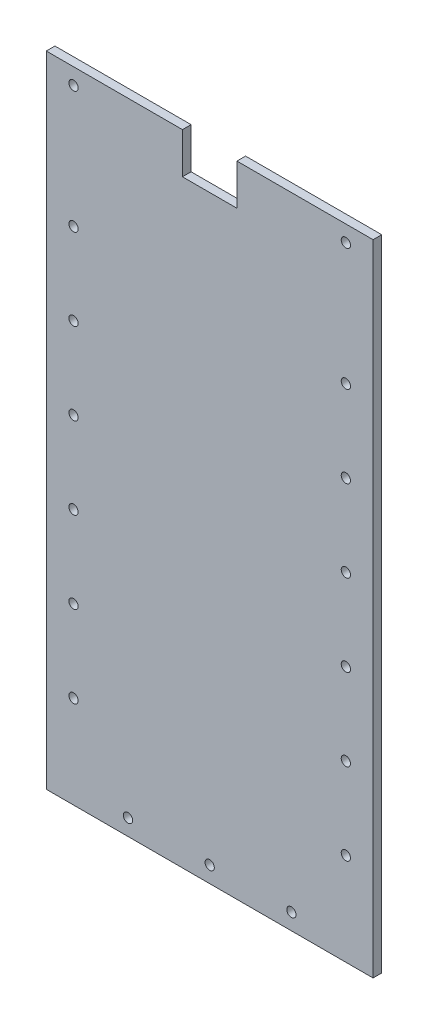
SolidWorks part; units mm, degrees
ref_plane "Front Plane" through (0, 0, 0) normal (0, 0, 1) x (1, 0, 0)
ref_plane "Top Plane" through (0, 0, 0) normal (0, 1, 0) x (1, 0, 0)
ref_plane "Right Plane" through (0, 0, 0) normal (1, 0, 0) x (0, 0, -1)
sketch "Sketch1" plane through (0, 0, 0) normal (0, 0, 1) x (1, 0, 0)
  line L1 (0, 0) -> (120, 0)
  line L2 (0, 0) -> (0, 234.78)
  line L3 (0, 234.78) -> (120, 234.78)
  line L4 (120, 0) -> (120, 234.78)
  dimension "D1" = 234.78
  dimension "D2" = 120
extrude "Boss-Extrude1" add sketch "Sketch1" along normal blind 3.175 contours L4 L3 L2 L1
sketch "Sketch2" plane through (0, 0, 3.175) normal (0, 0, 1) x (1, 0, 0)
  line L0 (60, 0) -> (60, 234.78) construction
  line L1 (0, 0) -> (120, 0) construction
  line L2 (0, 234.78) -> (120, 234.78) construction
  line L4 (50, 219.78) -> (70, 219.78)
  line L5 (50, 219.78) -> (50, 234.78)
  line L6 (50, 234.78) -> (70, 234.78)
  line L7 (70, 219.78) -> (70, 234.78)
  line L8 (50, 219.78) -> (70, 234.78) construction
  line L9 (50, 234.78) -> (70, 219.78) construction
  point P6 (60, 227.28)
  dimension "D1" = 20
  dimension "D2" = 15
extrude "Cut-Extrude1" cut sketch "Sketch2" against normal up to next
hole_wizard "Tap Drill for M3x0.5 Tap1" positions "Sketch3" profile "Sketch4" hole size "M3x0.5" standard "ANSI Metric"
sketch "Sketch3" plane through (42.9522, 18.5216, 3.175) normal (0, 0, 1) x (-1, 0, 0)
  point P0 (32.9522, -210.3133)
  point P3 (32.9522, -165.4784)
  point P9 (32.9522, -105.4784)
  point P12 (32.9522, -75.4784)
  point P15 (32.9522, -45.4784)
  point P18 (32.9522, -15.4784)
  point P22 (-67.0478, -210.3133)
  point P43 (32.9522, -135.4784)
  point P48 (12.9522, 12.5767)
  point P51 (-17.0478, 12.5767)
  point P54 (-47.0478, 12.5767)
  point P57 (-67.0478, -165.4784)
  point P59 (-67.0478, -135.4784)
  point P61 (-67.0478, -105.4784)
  point P63 (-67.0478, -75.4784)
  point P65 (-67.0478, -45.4784)
  point P69 (-67.0478, -15.4784)
sketch "Sketch4" plane through (10, 228.8349, 3.175) normal (1, 0, 0) x (0, -1, 0)
  line L0 (0, 0) -> (0, 3.18)
  line L1 (0, 3.18) -> (1.7, 3.18)
  line L2 (1.7, 3.18) -> (1.7, 0)
  line L3 (1.7, 0) -> (0, 0)
  line L4 (0, 3.18) -> (-1.7, 3.18) construction
  line L5 (0, -6.35) -> (0, 107.95) construction
  dimension "Hole Dia." = 3.4
  dimension "Hole Depth" = 3.18
  dimension "Drill Angle" = 180
